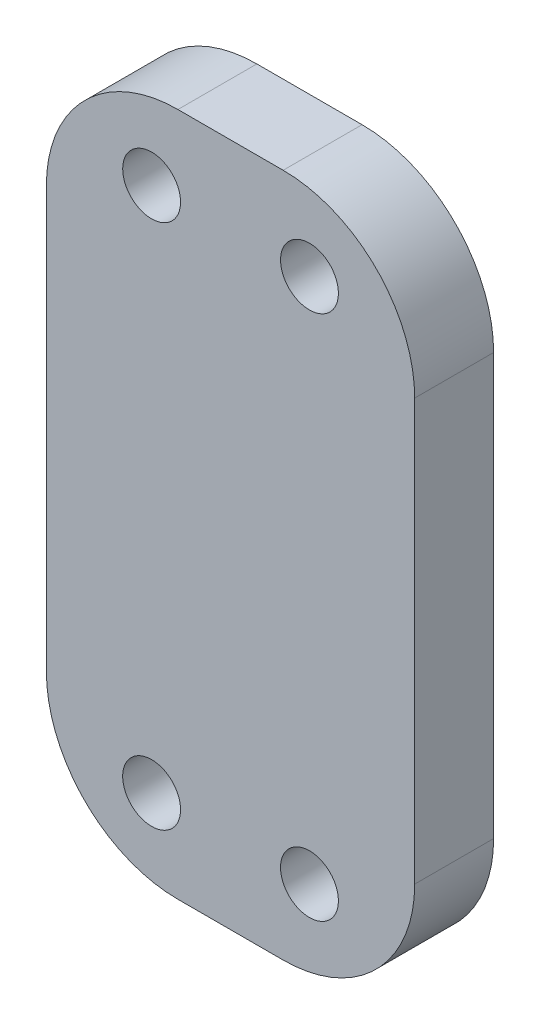
SolidWorks part; units mm, degrees
material "Polywood"
ref_plane "Front Plane" through (0, 0, 0) normal (0, 0, 1) x (1, 0, 0)
ref_plane "Top Plane" through (0, 0, 0) normal (0, 1, 0) x (1, 0, 0)
ref_plane "Right Plane" through (0, 0, 0) normal (1, 0, 0) x (0, 0, -1)
sketch "Sketch1" plane through (0, 0, 0) normal (0, 0, 1) x (1, 0, 0)
  line L0 (0, 0) -> (11343.5294, 0) construction
  line L1 (7, -13) -> (-7, -13)
  line L2 (7, -13) -> (7, 13)
  line L3 (7, 13) -> (-7, 13)
  line L4 (-7, -13) -> (-7, 13)
  line L5 (7, -13) -> (-7, 13) construction
  line L6 (7, 13) -> (-7, -13) construction
  line L7 (0, 0) -> (0, 11243.6489) construction
  circle A0 centre (3, 10) radius 1.1
  circle A1 centre (-3, 10) radius 1.1
  circle A2 centre (3, -10) radius 1.1
  circle A3 centre (-3, -10) radius 1.1
  point P0 (0, 0)
  dimension "D5" = 2.2
  dimension "D1" = 10
  dimension "D2" = 3
  dimension "D3" = 14
  dimension "D4" = 26
extrude "Boss-Extrude1" add sketch "Sketch1" along normal blind 3
fillet "Fillet1" radius 5 4 edges at (7, -13, 1.5) (-7, -13, 1.5) (7, 13, 1.5) (-7, 13, 1.5)
